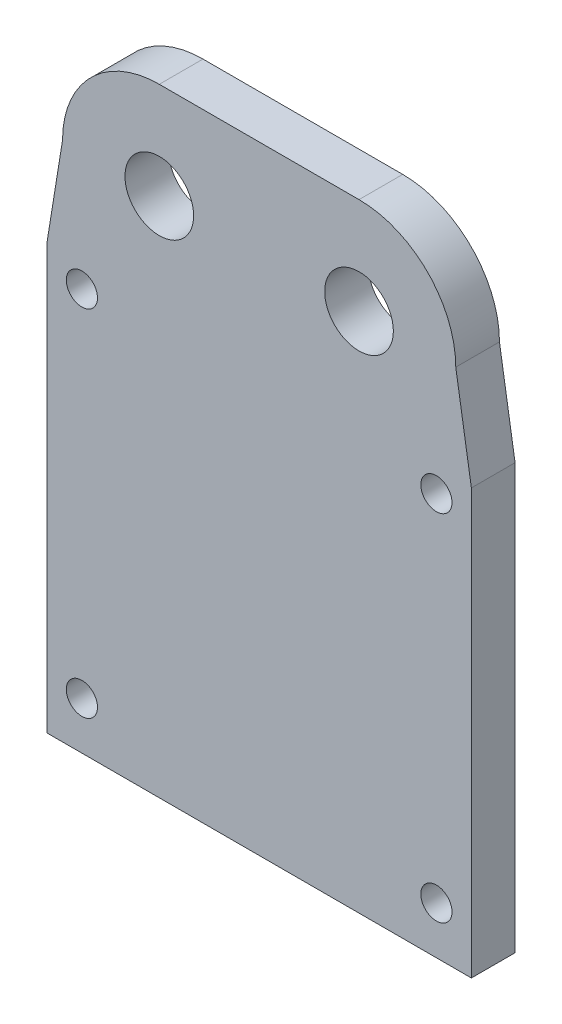
SolidWorks part; units mm, degrees
ref_plane "前视基准面" through (0, 0, 0) normal (0, 0, 1) x (1, 0, 0)
ref_plane "上视基准面" through (0, 0, 0) normal (0, 1, 0) x (1, 0, 0)
ref_plane "右视基准面" through (0, 0, 0) normal (1, 0, 0) x (0, 0, -1)
other "Configuration Table"
sketch "Sketch1" plane through (0, 0, 0) normal (0, 0, 1) x (1, 0, 0)
  line L0 (-8, 0) -> (8, 0) construction
  line L1 (-8, 7.75) -> (8, 7.75)
  line L2 (-8, -7.75) -> (8, -7.75)
  circle A0 centre (-8, 0) radius 2.75
  circle A1 centre (8, 0) radius 2.75
  circle A2 centre (-8, 0) radius 7.75
  circle A3 centre (8, 0) radius 7.75
  point P5 (0, 0)
  dimension "D2" = 5.5
  dimension "D3" = 5.5
  dimension "D1" = 16
  dimension "D4" = 5
extrude "Boss-Extrude1" add sketch "Sketch1" along normal blind 10
sketch "Sketch5" plane through (0, 0, 0) normal (0, 0, 1) x (1, 0, 0)
  line L0 (-15.75, 0) -> (-17, -7.75)
  line L1 (-17, -7.75) -> (17, -7.75)
  line L2 (17, -7.75) -> (15.75, 0)
  line L3 (-8, -7.75) -> (8, -7.75)
  line L4 (-12.5, -12.25) -> (-12.5, -37.25)
  line L5 (-17, -7.75) -> (17, -7.75)
  line L6 (-17, -7.75) -> (-17, -41.75)
  line L7 (-17, -41.75) -> (17, -41.75)
  line L8 (17, -7.75) -> (17, -41.75)
  line L9 (-12.5, -37.25) -> (12.5, -37.25)
  line L10 (12.5, -12.25) -> (12.5, -37.25)
  line L11 (-12.5, -12.25) -> (12.5, -12.25)
  line L12 (-12.5, -12.25) -> (-12.5, -7.75)
  line L13 (12.5, -12.25) -> (12.5, -7.75)
  arc A0 (-8, 7.75) -> (-8, -7.75) centre (-8, 0) ccw construction
  arc A1 (8, -7.75) -> (8, 7.75) centre (8, 0) ccw construction
  circle A2 centre (-8, 0) radius 7.75
  circle A3 centre (8, 0) radius 7.75
  point P20 (0, -7.75)
  dimension "D1" = 34
  dimension "D2" = 34
  dimension "D3" = 4.5
extrude "Boss-Extrude4" add sketch "Sketch5" along normal blind 10 contours L13 L10 L9 L4 L12 L1 L6 L7 L8 L5 | A2 L0 L1 L5 | A3 L1 L5 L2
sketch "Sketch7" plane through (0, 0, 10) normal (0, 0, 1) x (1, 0, 0)
  line L0 (12.5, -37.25) -> (12.5, -7.75) construction
  line L1 (-12.5, -7.75) -> (12.5, -7.75)
  line L2 (-12.5, -7.75) -> (-12.5, -5.75)
  line L3 (-12.5, -5.75) -> (12.5, -5.75)
  line L4 (12.5, -7.75) -> (12.5, -5.75)
  dimension "D1" = 2
extrude "Boss-Extrude6" add sketch "Sketch7" along normal blind 2
sketch "Sketch8" plane through (0, 0, 10) normal (0, 0, 1) x (1, 0, 0)
  line L0 (-12.5, -7.75) -> (12.5, -7.75) construction
  line L1 (-16, -7.75) -> (16, -7.75) construction
  line L2 (-16, -7.75) -> (-16, -39.75) construction
  line L3 (-16, -39.75) -> (16, -39.75) construction
  line L4 (16, -7.75) -> (16, -39.75) construction
  line L5 (0, -7.75) -> (0, -39.75) construction
  line L6 (-16, -23.75) -> (16, -23.75) construction
  circle A0 centre (-14.2, -9.55) radius 1.25
  circle A1 centre (14.2, -9.55) radius 1.25
  circle A2 centre (14.2, -37.95) radius 1.25
  circle A3 centre (-14.2, -37.95) radius 1.25
  point P6 (0, -7.75)
  dimension "D5" = 2.5
  dimension "D1" = 32
  dimension "D2" = 32
  dimension "D3" = 1.8
  dimension "D4" = 1.8
extrude "Cut-Extrude3" cut sketch "Sketch8" against normal blind 19
sketch "Sketch9" plane through (0, 0, 0) normal (0, 0, -1) x (-1, 0, 0)
  line L1 (-12.5, -7.75) -> (12.5, -7.75)
  line L2 (-12.5, -7.75) -> (-12.5, -37.25)
  line L3 (-12.5, -37.25) -> (12.5, -37.25)
  line L4 (12.5, -7.75) -> (12.5, -37.25)
extrude "Boss-Extrude7" add sketch "Sketch9" against normal blind 10
sketch "Sketch10" plane through (0, 7.75, 0) normal (0, 1, 0) x (1, 0, 0)
  line L0 (17, -10) -> (17, 0) construction
  line L1 (-17, 0) -> (17, 0)
  line L2 (-17, 0) -> (-17, -3.5)
  line L3 (-17, -3.5) -> (17, -3.5)
  line L4 (17, 0) -> (17, -3.5)
  line L7 (-17, -3.5) -> (17, -3.5)
  line L8 (-17, -3.5) -> (-17, -13.3039)
  line L9 (-17, -13.3039) -> (17, -13.3039)
  line L10 (17, -3.5) -> (17, -13.3039)
  line M10 (-8, 0) -> (-8, -10)
  line M11 (-8, -10) -> (8, -10)
  line M12 (8, -10) -> (8, 0)
  dimension "D1" = 3.5
extrude "Cut-Extrude4" cut sketch "Sketch10" against normal blind 54 contours L10 L3 L8 L9 M12 M11 M10 | L3 M10 M11 M12
